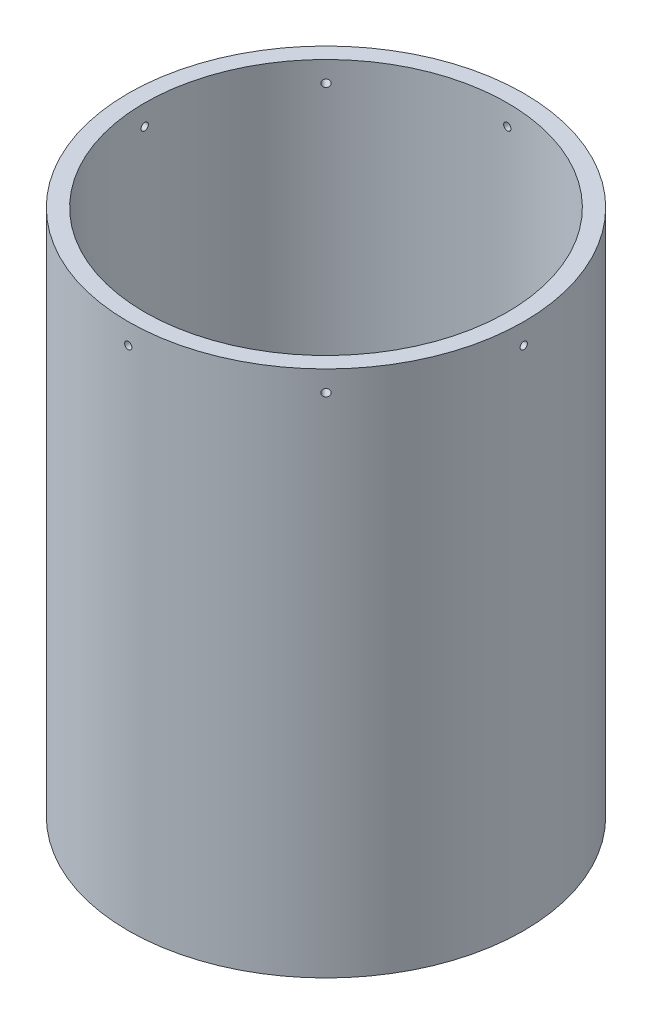
SolidWorks part; units mm, degrees
ref_plane "Front Plane" through (0, 0, 0) normal (0, 0, 1) x (1, 0, 0)
ref_plane "Top Plane" through (0, 0, 0) normal (0, 1, 0) x (1, 0, 0)
ref_plane "Right Plane" through (0, 0, 0) normal (1, 0, 0) x (0, 0, -1)
sketch "Sketch1" plane through (0, 0, 0) normal (0, 1, 0) x (1, 0, 0)
  circle A0 centre (0, 0) radius 139.7
  circle A1 centre (0, 0) radius 152.4
  dimension "D1" = 279.4
  dimension "D2" = 304.8
extrude "Boss-Extrude1" add sketch "Sketch1" along normal blind 406.4
ref_plane "Plane1" through (152.4, 0, 0) normal (1, 0, 0) x (0, 0, -1)
hole_wizard "#10 Clearance Hole1" positions "Sketch2" profile "Sketch3" hole size "#10" standard "ANSI Inch"
sketch "Sketch2" plane through (152.4, 0, 0) normal (1, 0, 0) x (0, 0, -1)
  line L0 (0, 390.525) -> (0, 0)
  line L2 (152.4, 406.4) -> (-152.4, 406.4) construction
  point P0 (0, 390.525)
  dimension "D1" = 15.875
sketch "Sketch3" plane through (152.4, 390.525, 0) normal (0, 1, 0) x (0, 0, -1)
  line L0 (0, 0) -> (0, 349.967)
  line L1 (0, 349.967) -> (2.8067, 349.967)
  line L2 (2.8067, 349.967) -> (2.8067, 0)
  line L5 (2.8067, 0) -> (0, 0)
  line L11 (0, -6.35) -> (0, 107.95) construction
  dimension "Thru Hole Dia." = 5.6134
  dimension "Thru Hole Depth" = 349.967
pattern_circular "CirPattern1" count 8 over 360 about axis through (0, 406.4, 0) along (0, 1, 0) of "#10 Clearance Hole1"
ref_plane "Plane2" through (0, 203.2, 0) normal (0, 1, 0) x (1, 0, 0)
sketch "Sketch4" plane through (152.4, 0, 0) normal (1, 0, 0) x (0, 0, -1)
  line L0 (152.4, 406.4) -> (-152.4, 406.4) construction
  circle A0 centre (0, 304.8) radius 12.7
  dimension "D1" = 25.4
  dimension "D2" = 101.6
ref_plane "Plane3" through (-107.7631, 0, -107.7631) normal (-0.7071, 0, -0.7071) x (0, -1, 0)
hole_wizard "#8-32 Tapped Hole1" positions "Sketch13" profile "Sketch14" tap size "#8-32" standard "ANSI Inch"
sketch "Sketch13" plane through (-107.7631, 0, -107.7631) normal (-0.7071, 0, -0.7071) x (0, -1, 0)
  line L0 (-127, -8.5725) -> (-127, 8.5725)
  line L1 (-127, 0) -> (0, 0)
  point P0 (-127, -8.5725)
  point P2 (-127, 8.5725)
  dimension "D1" = 17.145
  dimension "D2" = 127
sketch "Sketch14" plane through (-101.7014, 127, -113.8247) normal (0, 1, 0) x (-0.7071, 0, 0.7071)
  line L0 (0, 0) -> (0, 12.9633)
  line L1 (0, 12.9633) -> (1.7272, 12.9633)
  line L2 (1.7272, 12.9633) -> (1.7272, 0)
  line L5 (1.7272, 0) -> (0, 0)
  line L11 (0, -6.35) -> (0, 107.95) construction
  dimension "Thru Tap Drill Dia." = 3.4544
  dimension "Thru Tap Drill Depth" = 12.9633
cosmetic thread "Hole Thread5" parameters "D2"=4.1656
cosmetic thread "Hole Thread6" parameters "D2"=4.1656
